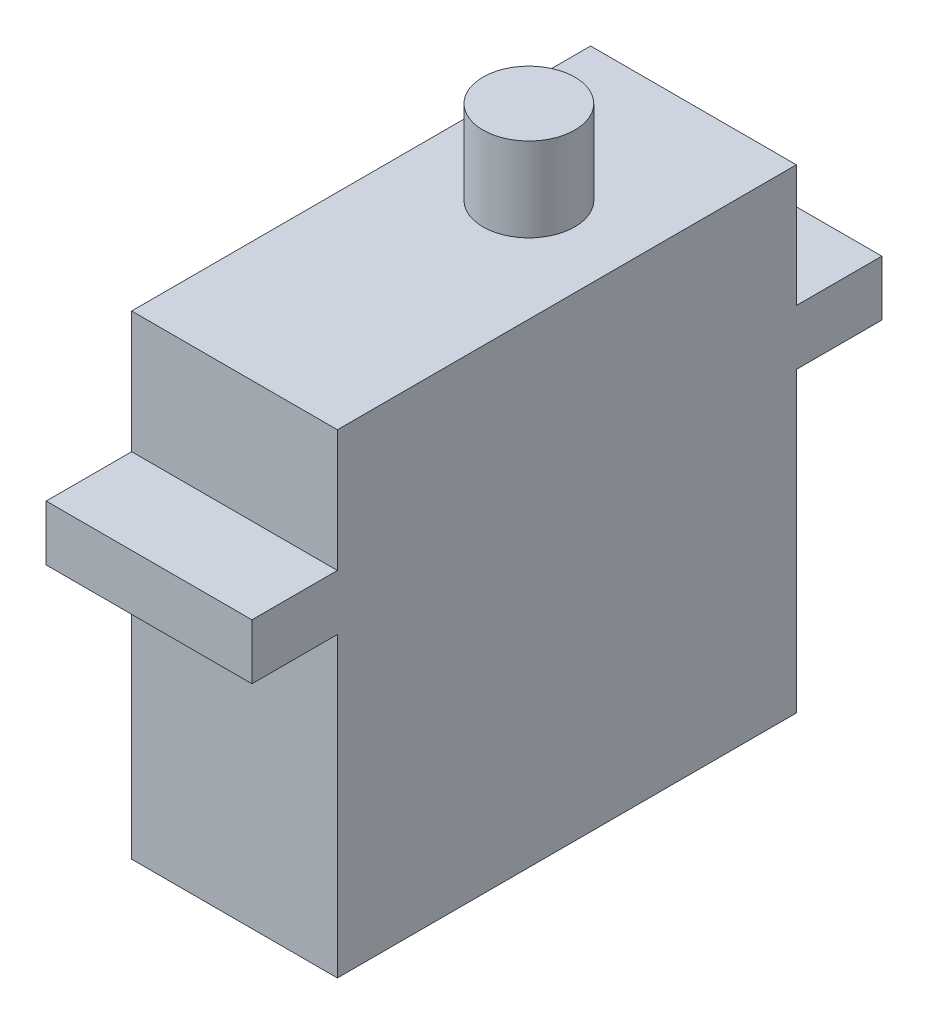
SolidWorks part; units mm, degrees
ref_plane "Front Plane" through (0, 0, 0) normal (0, 0, 1) x (1, 0, 0)
ref_plane "Top Plane" through (0, 0, 0) normal (0, 1, 0) x (1, 0, 0)
ref_plane "Right Plane" through (0, 0, 0) normal (1, 0, 0) x (0, 0, -1)
sketch "Sketch2" plane through (0, 0, 0) normal (1, 0, 0) x (0, 0, -1)
  line L1 (-14.5, 15) -> (14.5, 15)
  line L2 (-14.5, 15) -> (-14.5, -15)
  line L3 (-14.5, -15) -> (14.5, -15)
  line L4 (14.5, 15) -> (14.5, -15)
  line L5 (-14.5, 15) -> (14.5, -15) construction
  line L6 (-14.5, -15) -> (14.5, 15) construction
  line L7 (14.5, 7.3) -> (19.9, 7.3)
  line L8 (14.5, 7.3) -> (14.5, 3.8)
  line L9 (14.5, 3.8) -> (19.9, 3.8)
  line L10 (19.9, 7.3) -> (19.9, 3.8)
  line L11 (-14.5, 7.3) -> (-19.9, 7.3)
  line L12 (-14.5, 7.3) -> (-14.5, 3.8)
  line L13 (-14.5, 3.8) -> (-19.9, 3.8)
  line L14 (-19.9, 7.3) -> (-19.9, 3.8)
  line L16 (-19.9, 5.55) -> (19.9, 5.55) construction
  line L17 (1.2, 15) -> (7, 15)
  line L18 (1.2, 15) -> (1.2, 20.3)
  line L19 (1.2, 20.3) -> (7, 20.3)
  line L20 (7, 15) -> (7, 20.3)
  point P0 (0, 0)
  point P22 (0, 5.55)
  dimension "D1" = 22.3
  dimension "D2" = 29
  dimension "D3" = 35.3
  dimension "D4" = 39.8
  dimension "D5" = 30
  dimension "D6" = 3.5
  dimension "D7" = 5.8
  dimension "D8" = 7.5
extrude "Boss-Extrude1" add sketch "Sketch2" along normal blind 13 contours L4 L1 L2 L3 | L11 L14 L13 L2 | L1 L20 L19 L18 | L10 L7 L4 L9
sketch "Sketch3" plane through (0, 15, 0) normal (0, 1, 0) x (1, 0, 0)
  line L0 (13, 7) -> (0, 7) construction
  line L1 (13, 1.2) -> (9.4, 1.2)
  line L2 (13, 1.2) -> (13, 7)
  line L3 (13, 7) -> (9.4, 7)
  line L4 (9.4, 1.2) -> (9.4, 7)
  line L5 (13, 7) -> (0, 7) construction
  line L6 (0, 1.2) -> (3.6, 1.2)
  line L7 (0, 1.2) -> (0, 7)
  line L8 (0, 7) -> (3.6, 7)
  line L9 (3.6, 1.2) -> (3.6, 7)
  line L10 (13, 19.9) -> (0, 19.9) construction
  line L11 (9.4, 7) -> (3.6, 7)
  line L12 (9.4, 1.2) -> (3.6, 1.2)
  circle A0 centre (6.5, 4.1) radius 2.9
  point P15 (3.6, 4.1)
  point P21 (6.5, 19.9)
  line M7 (13, 1.2) -> (0, 1.2)
extrude "Cut-Extrude1" cut sketch "Sketch3" along normal up to surface (5.3 mm away) contours A0 L4 M7 | A0 L4 L11 | A0 L11 L9 | A0 L9 L12 | L9 L8 L7 M7 | L4 L2 L3 M7 up to face at (6.5, 20.3, -4.1)
